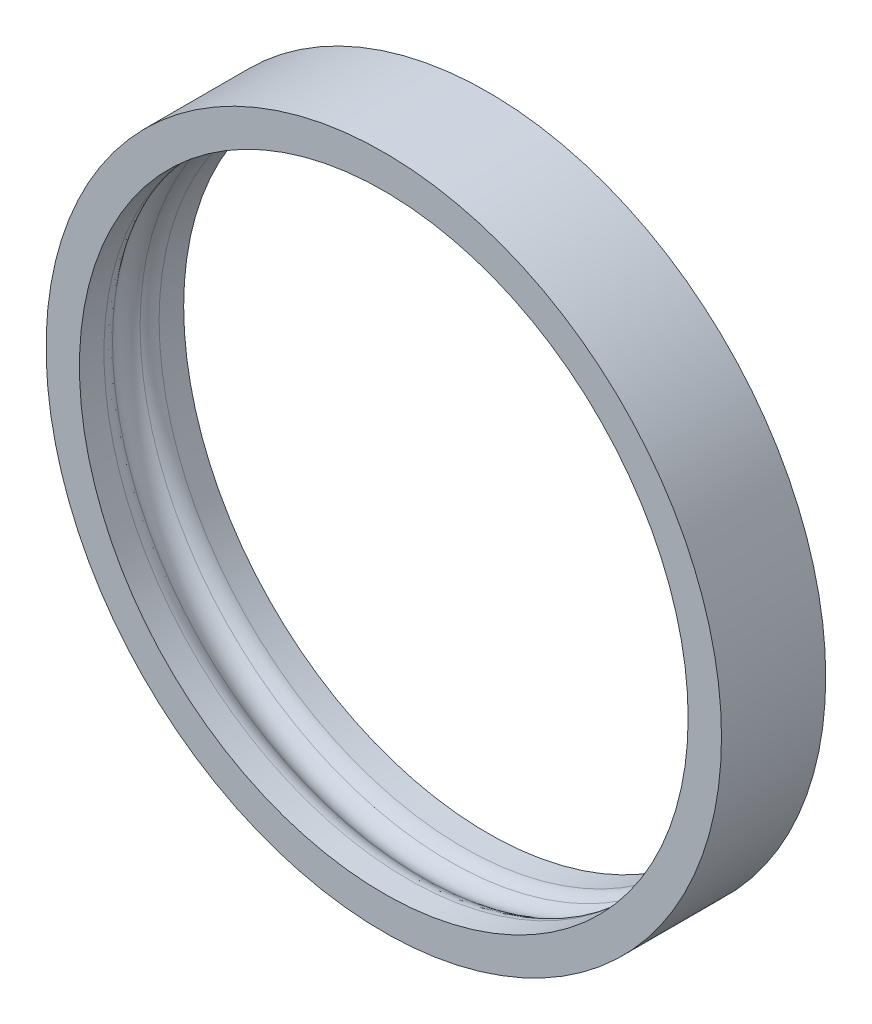
SolidWorks part; units mm, degrees
ref_plane "前视基准面" through (0, 0, 0) normal (0, 0, 1) x (1, 0, 0)
ref_plane "上视基准面" through (0, 0, 0) normal (0, 1, 0) x (1, 0, 0)
ref_plane "右视基准面" through (0, 0, 0) normal (1, 0, 0) x (0, 0, -1)
sketch "草图1" plane through (0, 0, 0) normal (0, 0, 1) x (1, 0, 0)
  circle A0 centre (0, 0) radius 14.6
  circle A1 centre (0, 0) radius 16.2
  dimension "D1" = 32.4
  dimension "D2" = 29.2
extrude "凸台-拉伸1" add sketch "草图1" along normal mid plane 5
sketch "草图3" plane through (0, 0, 0) normal (0, 1, 0) x (1, 0, 0)
  circle A0 centre (-14.1, 0) radius 1
  dimension "D1" = 2
  dimension "D2" = 14.1
revolve "切除-旋转1" cut sketch "草图3" angle 360 about axis through (0, 0, 2.5) along (0, 0, -1)
fillet "圆角1" radius 1 2 edges at (-14.6, 0, 0.866) (14.6, 0, -0.866)
equation "\"d\"= 32.4"
equation "\"D1@草图1\"=\"d\""
equation "\"d2\"= \"d\" - 3.2"
equation "\"D2@草图1\"=\"d2\""
equation "\"l1\"= \"d2\" / 2 - 0.5"
equation "\"D2@草图3\"=\"l1\""
